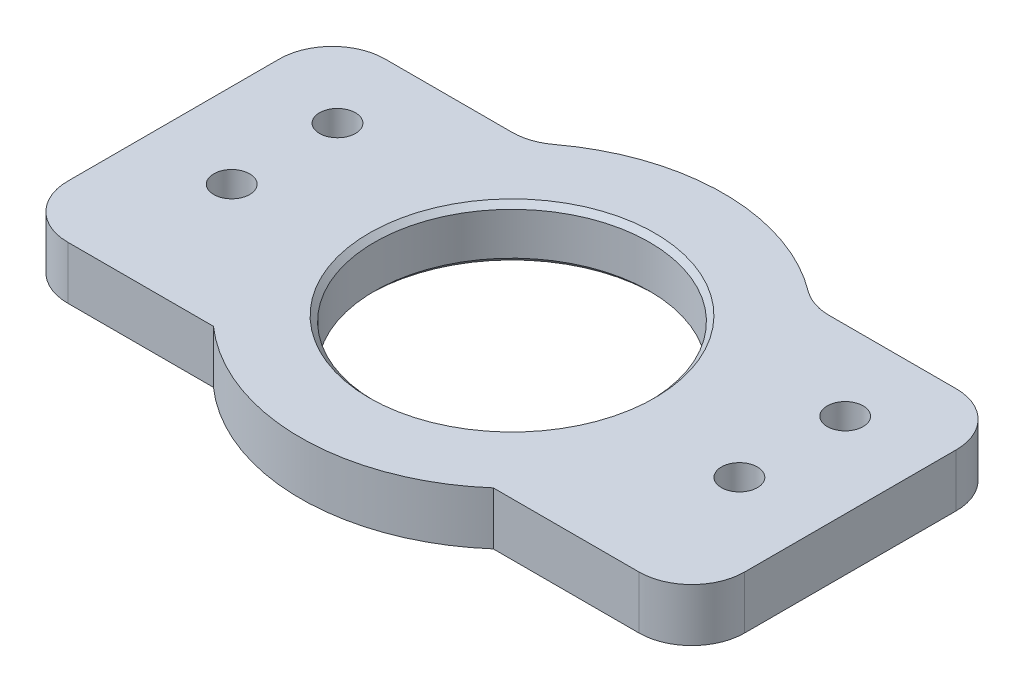
SolidWorks part; units mm, degrees
ref_plane "前视基准面" through (0, 0, 0) normal (0, 0, 1) x (1, 0, 0)
ref_plane "上视基准面" through (0, 0, 0) normal (0, 1, 0) x (1, 0, 0)
ref_plane "右视基准面" through (0, 0, 0) normal (1, 0, 0) x (0, 0, -1)
other "Configuration Table"
sketch "草图1" plane through (0, 0, 0) normal (0, 1, 0) x (1, 0, 0)
  line L0 (45.2288, 30) -> (64, 30)
  line L1 (0, 0) -> (18.7712, 0)
  line L2 (0, 0) -> (0, 30)
  line L3 (0, 30) -> (18.7712, 30)
  line L4 (64, 0) -> (64, 30)
  line L5 (45.2288, 0) -> (64, 0)
  arc A0 (18.7712, 0) -> (45.2288, 0) centre (32, 15) ccw
  arc A1 (45.2288, 30) -> (18.7712, 30) centre (32, 15) ccw
  dimension "D3" = 40
  dimension "D1" = 64
  dimension "D2" = 30
  dimension "D4" = 32
  dimension "D5" = 15
extrude "凸台-拉伸1" add sketch "草图1" along normal blind 5
sketch "草图2" plane through (0, 5, 0) normal (0, 1, 0) x (1, 0, 0)
  line L0 (0, 30) -> (0, 0) construction
  line L1 (0, 0) -> (18.7712, 0) construction
  circle A0 centre (32, 15) radius 13
  dimension "D1" = 26
  dimension "D2" = 32
  dimension "D3" = 15
extrude "切除-拉伸1" cut sketch "草图2" against normal blind 5
fillet "圆角1" radius 5 6 edges at (64, 2.5, -30) (64, 2.5, 0) (0, 2.5, 0) (0, 2.5, -30) (45.2288, 2.5, -30) (18.7712, 2.5, -30)
hole_wizard "M3 间隙孔1" positions "草图3" profile "草图4" hole size "M3" standard "GB" end condition through all
sketch "草图3" plane through (0, 0, 0) normal (0, -1, 0) x (-1, 0, 0)
  point P0 (-56, 22.5)
  point P3 (-56, 12.5)
  point P6 (-8, 22.5)
  point P9 (-8, 12.5)
sketch "草图4" plane through (56, 0, -22.5) normal (1, 0, 0) x (0, 0, -1)
  line L0 (0, 0) -> (0, 5)
  line L1 (0, 5) -> (1.7, 5)
  line L2 (1.7, 5) -> (1.7, 0)
  line L5 (1.7, 0) -> (0, 0)
  line L11 (0, -6.35) -> (0, 107.95) construction
  dimension "通孔孔直径" = 3.4
  dimension "通孔孔深度" = 5
chamfer "Chamfer1" distance 0.5 angle 45 2 edges at (32, 5, -2) (32, 0, -2)
